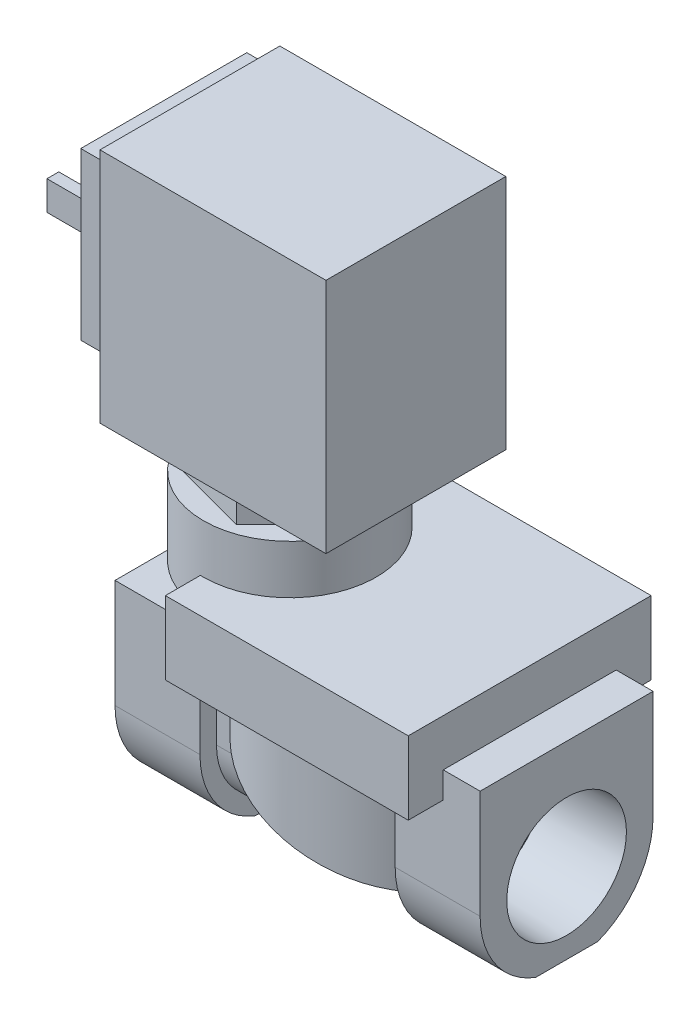
SolidWorks part; units mm, degrees
material "Brass"
ref_plane "Front" through (0, 0, 0) normal (0, 0, 1) x (1, 0, 0)
ref_plane "Top" through (0, 0, 0) normal (0, 1, 0) x (1, 0, 0)
ref_plane "Right" through (0, 0, 0) normal (1, 0, 0) x (0, 0, -1)
sketch "Sketch1" plane through (0, 0, 0) normal (0, 1, 0) x (1, 0, 0)
  circle A0 centre (0, 0) radius 18.0086
  dimension "D1" = 36.0172
extrude "Boss-Extrude1" add sketch "Sketch1" against normal blind 20.9296
sketch "Sketch2" plane through (0, 0, 0) normal (0, 0, 1) x (1, 0, 0)
  line L0 (-18.0086, -8.382) -> (18.0086, -20.9296)
  line L1 (-18.0086, 0) -> (-18.0086, -20.9296) construction
  line L2 (18.0086, -20.9296) -> (-18.0086, -20.9296)
  line L3 (-18.0086, -20.9296) -> (-18.0086, -8.382)
  line L4 (18.0086, 0) -> (-18.0086, 0) construction
  dimension "D1" = 8.382
extrude "Cut-Extrude1" cut sketch "Sketch2" against normal through all and the other way through all
sketch "Sketch3" plane through (0, 0, 0) normal (1, 0, 0) x (0, 0, -1)
  line L0 (-11.557, 0) -> (-11.557, -13.589)
  line L2 (11.557, -13.589) -> (11.557, 0)
  line L3 (11.557, 0) -> (-11.557, 0)
  line L6 (18.0086, 0) -> (-18.0086, 0) construction
  arc A1 (-11.557, -13.589) -> (11.557, -13.589) centre (0, -13.589) ccw
  dimension "D1" = 25.146
  dimension "D2" = 23.114
extrude "Boss-Extrude2" add sketch "Sketch3" along normal mid plane 32.258
sketch "Sketch5" plane through (-16.129, 0, 0) normal (-1, 0, 0) x (0, 0, 1)
  line L0 (-14.2875, 4.318) -> (-14.2875, -13.589)
  line L1 (14.2875, -13.589) -> (14.2875, 4.318)
  line L2 (14.2875, 4.318) -> (-14.2875, 4.318)
  line L3 (18.0086, 0) -> (11.557, 0) construction
  line L4 (-5.1294, -26.924) -> (5.1294, -26.924)
  arc A0 (-14.2875, -13.589) -> (-5.1294, -26.924) centre (0, -13.589) ccw
  arc A1 (5.1294, -26.924) -> (14.2875, -13.589) centre (0, -13.589) ccw
  dimension "D1" = 4.318
  dimension "D2" = 28.575
  dimension "D3" = 31.242
extrude "Boss-Extrude3" add sketch "Sketch5" along normal blind 14.0335
mirror "Mirror1" about plane through (0, 0, 0) normal (1, 0, 0) of "Boss-Extrude3"
sketch "Sketch6" plane through (0, 0, 0) normal (0, 1, 0) x (1, 0, 0)
  line L0 (30.1625, -14.2875) -> (30.1625, 14.2875) construction
  line L1 (-16.0655, -20.066) -> (24.0665, -20.066)
  line L2 (-16.0655, -20.066) -> (-16.0655, 20.066)
  line L3 (-16.0655, 20.066) -> (24.0665, 20.066)
  line L4 (24.0665, -20.066) -> (24.0665, 20.066)
  line L5 (-16.0655, -20.066) -> (24.0665, 20.066) construction
  line L6 (-16.0655, 20.066) -> (24.0665, -20.066) construction
  line L7 (0, 0) -> (24.0665, 0) construction
  point P0 (0, 0)
  dimension "D1" = 6.096
  dimension "D2" = 40.132
extrude "Boss-Extrude4" add sketch "Sketch6" along normal blind 12.0777
sketch "Sketch7" plane through (0, 12.0777, 0) normal (0, 1, 0) x (1, 0, 0)
  line L0 (0, 0) -> (-15.5674, 0) construction
  circle A0 centre (-15.5674, 0) radius 14.2875
  dimension "D1" = 28.575
extrude "Boss-Extrude5" add sketch "Sketch7" along normal blind 8.0772 and the other way blind 4.826
hole_wizard "1/2 NPT Tapped Hole1" positions "Sketch9" profile "Sketch8" size "1/2" standard "Ansi Inch"
sketch "Sketch9" plane through (30.1625, 0, 0) normal (1, 0, 0) x (0, 0, -1)
  point P0 (0, -13.589)
sketch "Sketch8" plane through (30.1625, -13.589, 0) normal (0, 1, 0) x (0, 0, -1)
  line L0 (0, 0) -> (0, 28.0036)
  line L1 (8.9281, 22.639) -> (0, 28.0036)
  line L2 (-8.9281, 22.639) -> (0, 28.0036) construction
  line L3 (8.9281, 22.639) -> (8.9281, 13.5712)
  line L4 (8.9281, 13.5712) -> (9.4797, 13.5712)
  line L5 (9.4797, 13.5712) -> (9.8861, 0)
  line L6 (-9.4797, 13.5712) -> (-9.8861, 0) construction
  line L7 (9.8861, 0) -> (0, 0)
  line L8 (0, -6.35) -> (0, 107.95) construction
  line L11 (-8.9281, 13.5712) -> (-9.4797, 13.5712) construction
  dimension "Tap Drill Dia." = 17.8562
  dimension "Tap Drill Depth" = 22.639
  dimension "Thread Dia." = 19.7721
  dimension "Thread Angle" = 3.43
  dimension "Thread Depth" = 13.5712
  dimension "Drill Angle" = 118
cosmetic thread "Hole Thread1" parameters "D1"=13.5712
mirror "Mirror2" about plane through (0, 0, 0) normal (1, 0, 0) of "1/2 NPT Tapped Hole1"
sketch "Sketch10" plane through (0, 20.1549, 0) normal (0, 1, 0) x (1, 0, 0)
  line L1 (-6.7165, 8.881) -> (-18.8331, 12.1056)
  line L2 (-18.8331, 12.1056) -> (-27.684, 3.2246)
  line L3 (-27.684, 3.2246) -> (-24.4182, -8.881)
  line L4 (-24.4182, -8.881) -> (-12.3017, -12.1056)
  line L5 (-12.3017, -12.1056) -> (-3.4508, -3.2246)
  line L6 (-3.4508, -3.2246) -> (-6.7165, 8.881)
  circle A0 centre (-15.5674, 0) radius 10.8585 construction
  dimension "D1" = 21.717
extrude "Boss-Extrude6" add sketch "Sketch10" along normal blind 5.9817
sketch "Sketch11" plane through (0, 26.1366, 0) normal (0, 1, 0) x (1, 0, 0)
  line L1 (-36.3954, -14.859) -> (5.2606, -14.859)
  line L2 (-36.3954, -14.859) -> (-36.3954, 14.859)
  line L3 (-36.3954, 14.859) -> (5.2606, 14.859)
  line L4 (5.2606, -14.859) -> (5.2606, 14.859)
  line L5 (-36.3954, -14.859) -> (5.2606, 14.859) construction
  line L6 (-36.3954, 14.859) -> (5.2606, -14.859) construction
  point P0 (-15.5674, 0)
  dimension "D1" = 29.718
  dimension "D2" = 41.656
extrude "Boss-Extrude7" add sketch "Sketch11" along normal blind 39.116
sketch "Sketch12" plane through (-36.3954, 0, 0) normal (-1, 0, 0) x (0, 0, 1)
  line L0 (0, 65.2526) -> (0, 62.7126) construction
  line L1 (-13.716, 35.2806) -> (13.716, 35.2806)
  line L2 (-13.716, 35.2806) -> (-13.716, 62.7126)
  line L3 (-13.716, 62.7126) -> (13.716, 62.7126)
  line L4 (13.716, 35.2806) -> (13.716, 62.7126)
  line L5 (-13.716, 35.2806) -> (13.716, 62.7126) construction
  line L6 (-13.716, 62.7126) -> (13.716, 35.2806) construction
  line L7 (-14.859, 65.2526) -> (14.859, 65.2526) construction
  line L12 (-14.859, 26.1366) -> (14.859, 26.1366)
  line L13 (14.859, 26.1366) -> (14.859, 65.2526)
  line L14 (14.859, 65.2526) -> (-14.859, 65.2526)
  line L15 (-14.859, 65.2526) -> (-14.859, 26.1366)
  line L16 (-14.859, 26.1366) -> (14.859, 26.1366)
  line L17 (14.859, 26.1366) -> (14.859, 65.2526)
  line L18 (14.859, 65.2526) -> (-14.859, 65.2526)
  line L19 (-14.859, 65.2526) -> (-14.859, 26.1366)
  point P0 (0, 48.9966)
  dimension "D1" = 27.432
  dimension "D2" = 2.54
  dimension "D3" = 0
extrude "Cut-Extrude2" cut sketch "Sketch12" against normal blind 4.318
sketch "Sketch13" plane through (-36.3954, 0, 0) normal (-1, 0, 0) x (0, 0, 1)
  line L0 (-7.1882, 51.0286) -> (-9.144, 51.0286)
  line L1 (-9.144, 51.0286) -> (-9.144, 46.2026)
  line L2 (-9.144, 46.2026) -> (-7.1882, 46.2026)
  line L3 (-7.1882, 50.2666) -> (-8.382, 50.2666)
  line L4 (-8.382, 50.2666) -> (-8.382, 46.9646)
  line L5 (-8.382, 46.9646) -> (-7.1882, 46.9646)
  line L6 (-7.1882, 51.0286) -> (-7.1882, 50.2666)
  line L7 (-7.1882, 46.9646) -> (-7.1882, 46.2026)
  line L8 (0, 62.7126) -> (0, 39.3534) construction
  line L9 (13.716, 62.7126) -> (-13.716, 62.7126) construction
  line L10 (13.716, 62.7126) -> (-13.716, 62.7126) construction
  line L11 (7.1882, 46.9646) -> (7.1882, 46.2026)
  line L16 (7.1882, 51.0286) -> (7.1882, 50.2666)
  line L17 (8.382, 46.9646) -> (7.1882, 46.9646)
  line L18 (8.382, 50.2666) -> (8.382, 46.9646)
  line L19 (7.1882, 50.2666) -> (8.382, 50.2666)
  line L20 (9.144, 46.2026) -> (7.1882, 46.2026)
  line L21 (9.144, 51.0286) -> (9.144, 46.2026)
  line L22 (7.1882, 51.0286) -> (9.144, 51.0286)
  dimension "D1" = 0.762
  dimension "D2" = 4.826
  dimension "D3" = 1.9558
  dimension "D4" = 11.684
  dimension "D5" = 18.288
extrude "Boss-Extrude8" add sketch "Sketch13" along normal blind 10.16
